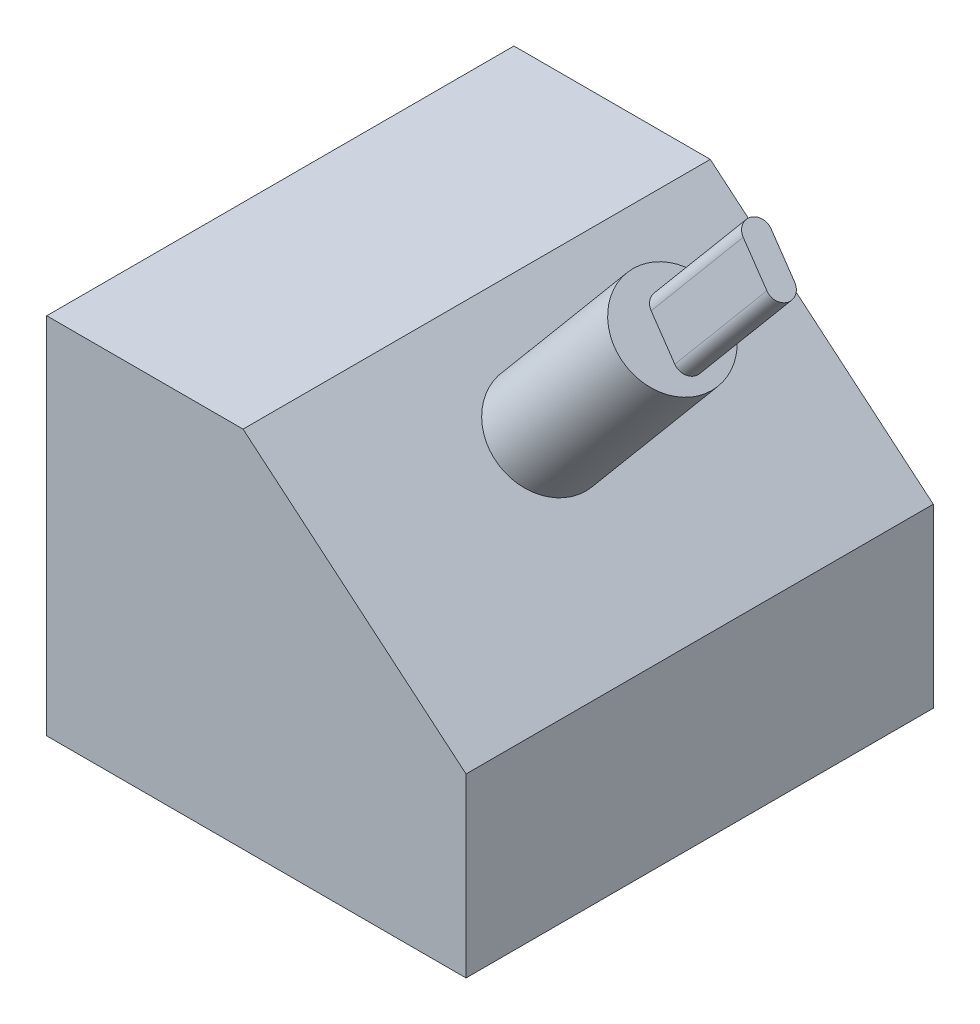
SolidWorks part; units mm, degrees
ref_plane "Front Plane" through (0, 0, 0) normal (0, 0, 1) x (1, 0, 0)
ref_plane "Top Plane" through (0, 0, 0) normal (0, 1, 0) x (1, 0, 0)
ref_plane "Right Plane" through (0, 0, 0) normal (1, 0, 0) x (0, 0, -1)
sketch "Sketch1" plane through (0, 0, 0) normal (0, 0, 1) x (1, 0, 0)
  line L0 (0, 0) -> (0, 48.2811)
  line L1 (0, 48.2811) -> (26.0538, 48.2811)
  line L2 (26.0538, 48.2811) -> (55.644, 23.4465)
  line L3 (55.644, 23.4465) -> (55.644, 0)
  line L4 (55.644, 0) -> (0, 0)
extrude "Boss-Extrude1" add sketch "Sketch1" along normal blind 62
sketch "Sketch2" plane through (34.5424, 41.1568, 0) normal (0.6429, 0.766, 0) x (0.766, -0.6429, 0)
  circle A0 centre (3.2864, -32.741) radius 6.829
extrude "Boss-Extrude2" add sketch "Sketch2" along normal blind 26
sketch "Sketch3" plane through (51.257, 61.0722, 0) normal (0.6429, 0.766, 0) x (0.766, -0.6429, 0)
  line L0 (6.5423, -33.0738) -> (1.0689, -32.0185) construction
  line L1 (6.2316, -34.685) -> (0.7583, -33.6297)
  line L2 (6.8529, -31.4627) -> (1.3796, -30.4073)
  arc A0 (6.2316, -34.685) -> (6.8529, -31.4627) centre (6.5423, -33.0738) ccw
  arc A1 (1.3796, -30.4073) -> (0.7583, -33.6297) centre (1.0689, -32.0185) ccw
  point P2 (3.8056, -32.5462)
extrude "Boss-Extrude3" add sketch "Sketch3" along normal blind 19
